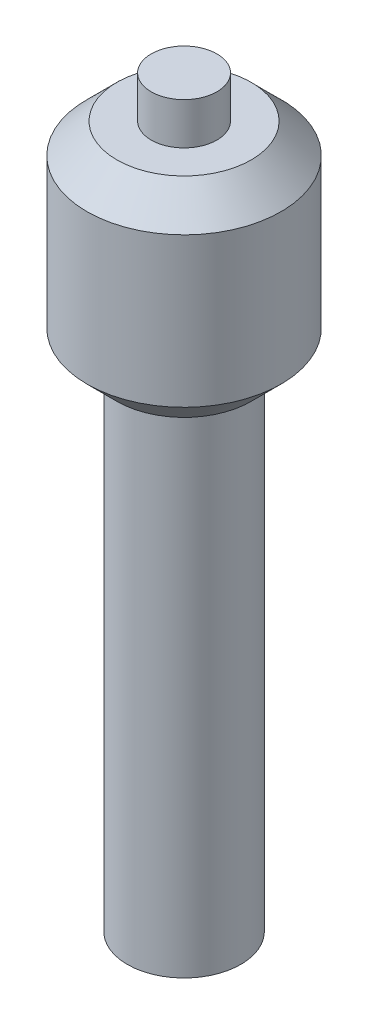
SolidWorks part; units mm, degrees
ref_plane "Front Plane" through (0, 0, 0) normal (0, 0, 1) x (1, 0, 0)
ref_plane "Top Plane" through (0, 0, 0) normal (0, 1, 0) x (1, 0, 0)
ref_plane "Right Plane" through (0, 0, 0) normal (1, 0, 0) x (0, 0, -1)
sketch "Sketch1" plane through (0, 0, 0) normal (0, 0, 1) x (1, 0, 0)
  line L0 (0, 309.182) -> (0, -398.661) construction
  line L1 (11, 264.4425) -> (0, 264.4425)
  line L2 (11, 264.4425) -> (11, 250.4425)
  line L3 (11, 250.4425) -> (22.5, 250.4425)
  line L4 (22.5, 250.4425) -> (32.5, 240.4425)
  line L5 (32.5, 240.4425) -> (32.5, 190.4425)
  line L6 (32.5, 190.4425) -> (22.5, 180.4425)
  line L7 (22.5, 180.4425) -> (19, 180.4425)
  line L8 (19, 180.4425) -> (19, 15.4425)
  line L9 (0, 15.4425) -> (19, 15.4425)
  line L10 (0, 15.4425) -> (0, 264.4425)
  dimension "D2" = 14
  dimension "D3" = 22.5
  dimension "D4" = 10
  dimension "D5" = 32.5
  dimension "D6" = 50
  dimension "D7" = 10
  dimension "D8" = 22.5
  dimension "D9" = 3.5
  dimension "D10" = 165
revolve "Revolve1" add sketch "Sketch1" angle 360 about L0
